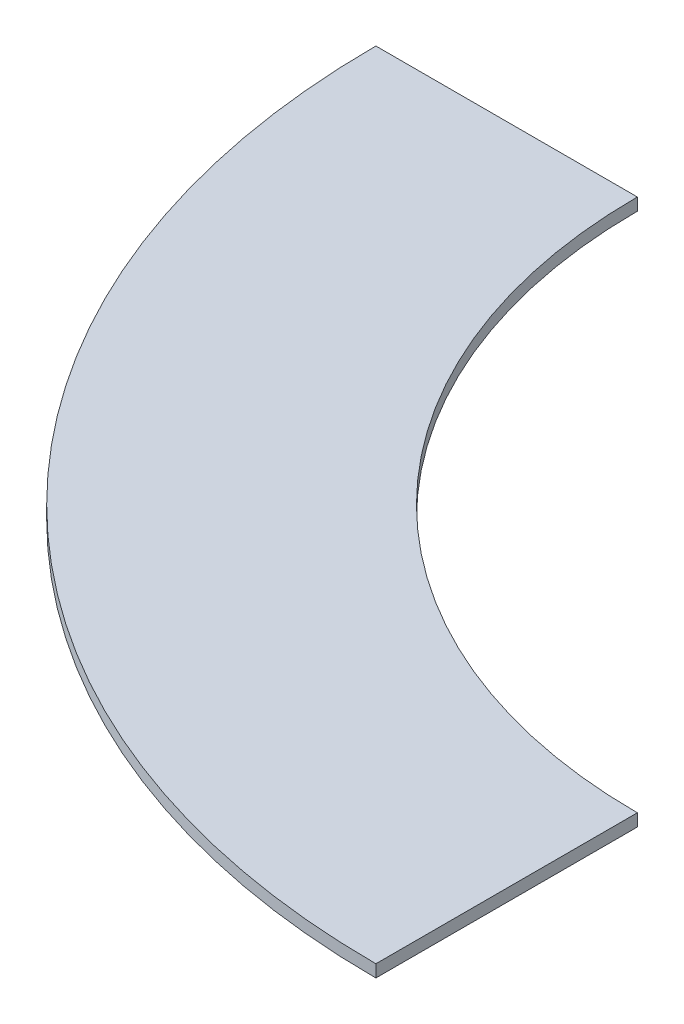
SolidWorks part; units mm, degrees
ref_plane "Front Plane" through (0, 0, 0) normal (0, 0, 1) x (1, 0, 0)
ref_plane "Top Plane" through (0, 0, 0) normal (0, 1, 0) x (1, 0, 0)
ref_plane "Right Plane" through (0, 0, 0) normal (1, 0, 0) x (0, 0, -1)
sketch "Sketch1" plane through (0, 0, 0) normal (0, 1, 0) x (1, 0, 0)
  line L0 (-342.9635, 0) -> (-511.1115, 0)
  line L1 (0, 342.9635) -> (0, 511.1115)
  line L2 (342.9635, 0) -> (511.1115, 0)
  line L3 (0, -342.9635) -> (0, -511.1115)
  circle A0 centre (0, 0) radius 511.1115
  circle A1 centre (0, 0) radius 342.9635
  point P6 (0, 0)
  point P7 (0, 0)
  point P8 (0, 0)
  point P15 (0, 0)
  dimension "D1" = 685.927
  dimension "D2" = 168.148
  dimension "D3" = 4
extrude "Boss-Extrude1" add sketch "Sketch1" along normal blind 7.9375 contours A1 L0 A0 L3
